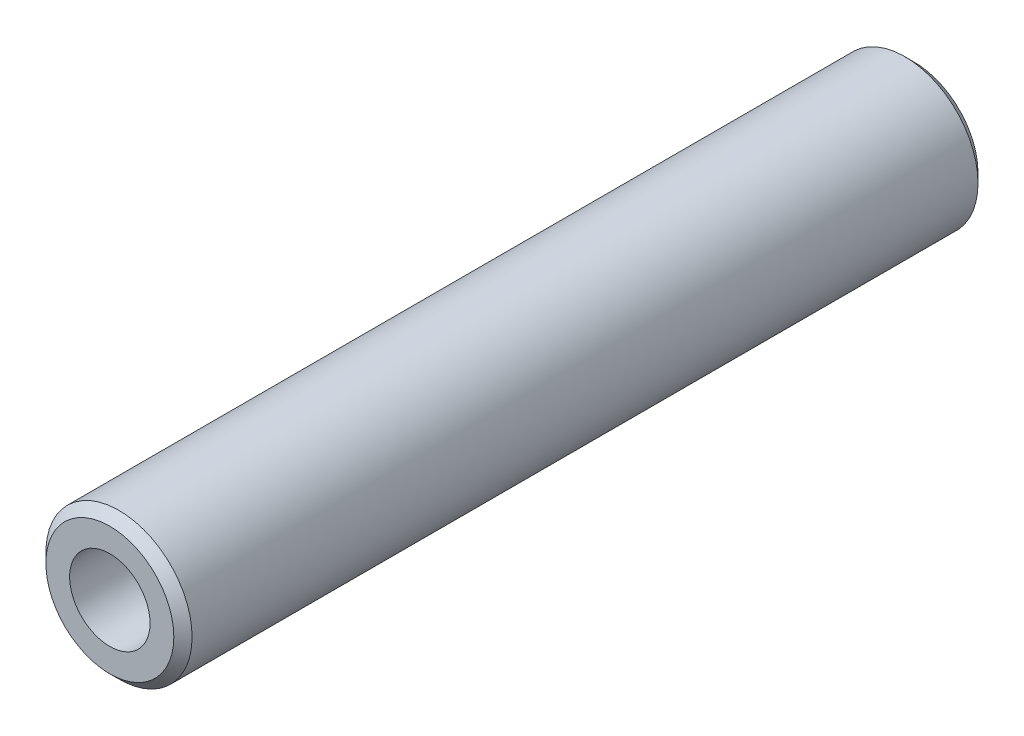
SolidWorks part; units mm, degrees
material "POM copolymère d'acétal"
ref_plane "Plan de face" through (0, 0, 0) normal (0, 0, 1) x (1, 0, 0)
ref_plane "Plan de dessus" through (0, 0, 0) normal (0, 1, 0) x (1, 0, 0)
ref_plane "Plan de droite" through (0, 0, 0) normal (1, 0, 0) x (0, 0, -1)
sketch "Esquisse1" plane through (0, 0, 0) normal (0, 0, 1) x (1, 0, 0)
  circle A0 centre (0, 0) radius 2.2
  circle A1 centre (0, 0) radius 4
  dimension "D1" = 4.4
  dimension "D2" = 8
extrude "Boss.-Extru.1" add sketch "Esquisse1" along normal mid plane 44
chamfer "Chamfer1" distance 0.5 angle 45 2 edges at (4, 0, -22) (4, 0, 22)
